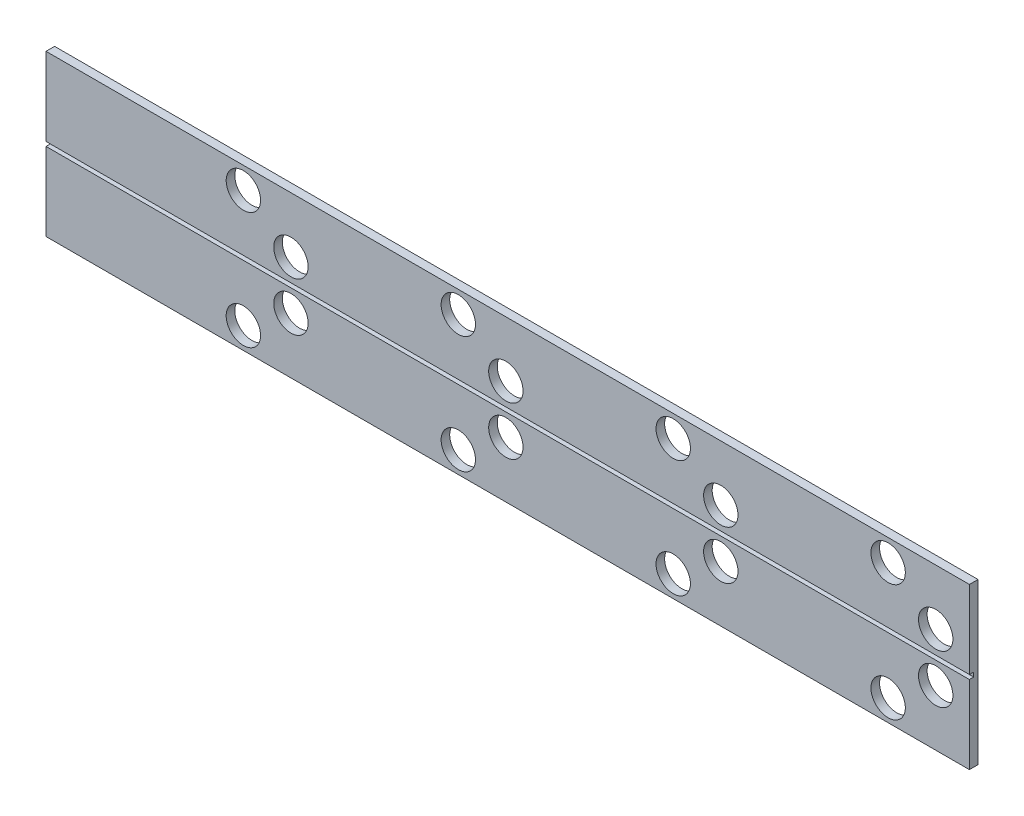
SolidWorks part; units mm, degrees
ref_plane "Ebene vorne" through (0, 0, 0) normal (0, 0, 1) x (1, 0, 0)
ref_plane "Ebene oben" through (0, 0, 0) normal (0, 1, 0) x (1, 0, 0)
ref_plane "Ebene rechts" through (0, 0, 0) normal (1, 0, 0) x (0, 0, -1)
sketch "Skizze1" plane through (0, 0, 0) normal (0, 0, 1) x (1, 0, 0)
  line L1 (-10.7411, 1.866) -> (10.7411, 1.866)
  line L2 (-10.7411, 1.866) -> (-10.7411, -1.866)
  line L3 (-10.7411, -1.866) -> (10.7411, -1.866)
  line L4 (10.7411, 1.866) -> (10.7411, -1.866)
  line L5 (-10.7411, 1.866) -> (10.7411, -1.866) construction
  line L6 (-10.7411, -1.866) -> (10.7411, 1.866) construction
  point P0 (0, 0)
extrude "Aufsatz-Linear austragen1" add sketch "Skizze1" along normal blind 0.2
sketch "Skizze2" plane through (0, 0, 0.2) normal (0, 0, 1) x (1, 0, 0)
  line L0 (-10.7411, 1.866) -> (-10.7411, -1.866) construction
  line L1 (10.7411, -0.05) -> (-10.7411, -0.05)
  line L2 (10.7411, -0.05) -> (10.7411, 0.05)
  line L3 (10.7411, 0.05) -> (-10.7411, 0.05)
  line L4 (-10.7411, -0.05) -> (-10.7411, 0.05)
  line L5 (10.7411, -0.05) -> (-10.7411, 0.05) construction
  line L6 (10.7411, 0.05) -> (-10.7411, -0.05) construction
  point P0 (0, 0)
  dimension "D1" = 0.1
extrude "Schnitt-Linear austragen1" cut sketch "Skizze2" against normal blind 0.1
sketch "Skizze3" plane through (0, 0, 0.2) normal (0, 0, 1) x (1, 0, 0)
  circle A0 centre (9.9572, -0.5629) radius 0.4
  circle A1 centre (8.8506, -1.3652) radius 0.4
  circle A2 centre (9.9572, 0.5713) radius 0.4
  circle A3 centre (8.8506, 1.3597) radius 0.4
extrude "Schnitt-Linear austragen2" cut sketch "Skizze3" against normal through all
pattern_linear "Lineares Muster1" count 4 spacing 5 along (-1, 0, 0) of "Schnitt-Linear austragen2"
